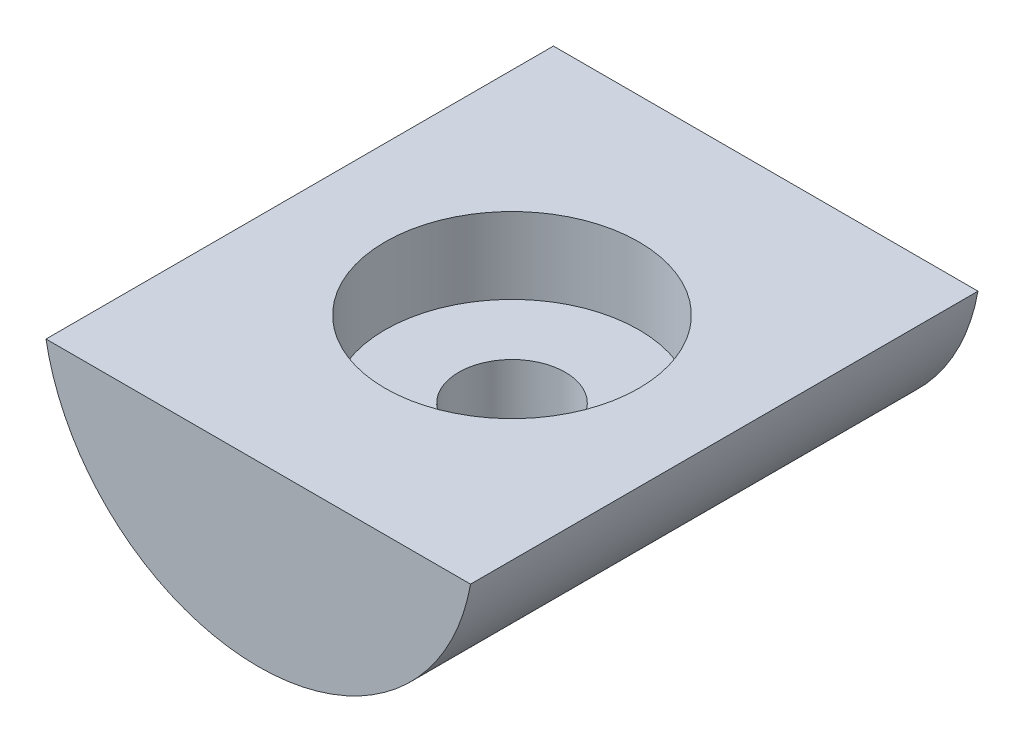
SolidWorks part; units mm, degrees
ref_plane "Front Plane" through (0, 0, 0) normal (0, 0, 1) x (1, 0, 0)
ref_plane "Top Plane" through (0, 0, 0) normal (0, 1, 0) x (1, 0, 0)
ref_plane "Right Plane" through (0, 0, 0) normal (1, 0, 0) x (0, 0, -1)
sketch "Sketch1" plane through (0, 0, 0) normal (0, 0, 1) x (1, 0, 0)
  line L0 (-8.3666, -1.5) -> (8.3666, -1.5)
  arc A0 (-8.3666, -1.5) -> (8.3666, -1.5) centre (0, 0) ccw
  dimension "D1" = 17
  dimension "D2" = 1.5
extrude "Boss-Extrude1" add sketch "Sketch1" along normal blind 20
sketch "Sketch2" plane through (0, -1.5, 0) normal (0, 1, 0) x (1, 0, 0)
  circle A0 centre (0, -10) radius 2.1
  dimension "D2" = 4.2
  dimension "D1" = 10
extrude "Cut-Extrude1" cut sketch "Sketch2" against normal through all
sketch "Sketch3" plane through (0, -1.5, 0) normal (0, 1, 0) x (1, 0, 0)
  circle A0 centre (0, -10) radius 5
  dimension "D1" = 10
extrude "Cut-Extrude2" cut sketch "Sketch3" against normal blind 3
